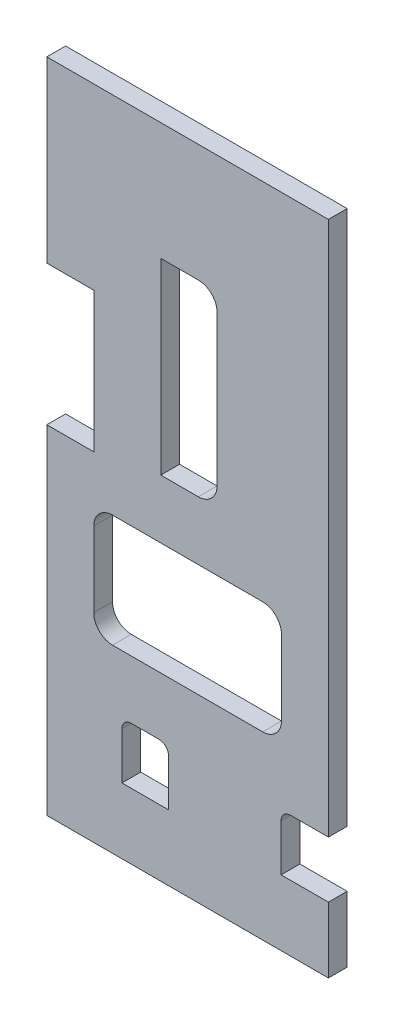
SolidWorks part; units mm, degrees
ref_plane "Front Plane" through (0, 0, 0) normal (0, 0, 1) x (1, 0, 0)
ref_plane "Top Plane" through (0, 0, 0) normal (0, 1, 0) x (1, 0, 0)
ref_plane "Right Plane" through (0, 0, 0) normal (1, 0, 0) x (0, 0, -1)
sketch "Sketch1" plane through (0, 0, 0) normal (0, 0, 1) x (1, 0, 0)
  line L1 (0, 0) -> (95.25, 0)
  line L2 (0, 0) -> (0, 222.25)
  line L3 (0, 222.25) -> (95.25, 222.25)
  line L4 (95.25, 0) -> (95.25, 222.25)
  dimension "D1" = 222.25
  dimension "D2" = 95.25
extrude "Boss-Extrude1" add sketch "Sketch1" along normal blind 6.35
sketch "Sketch2" plane through (0, 0, 0) normal (-1, 0, 0) x (0, 0, 1)
  line L1 (-4.1786, 161.8121) -> (13.515, 161.8121)
  line L2 (-4.1786, 161.8121) -> (-4.1786, 114.4656)
  line L3 (-4.1786, 114.4656) -> (13.515, 114.4656)
  line L4 (13.515, 161.8121) -> (13.515, 114.4656)
extrude "Cut-Extrude1" cut sketch "Sketch2" against normal blind 15.875
sketch "Sketch3" plane through (0, 0, 0) normal (0, 0, -1) x (-1, 0, 0)
  line L0 (-32.2, 118.9831) -> (-38.55, 118.9831) construction
  line L1 (-51.25, 182.4831) -> (-38.55, 182.4831)
  line L2 (-57.6, 176.1331) -> (-57.6, 125.3331)
  line L3 (-51.25, 118.9831) -> (-38.55, 118.9831)
  line L4 (-38.55, 182.4831) -> (-38.55, 118.9831)
  line L5 (-32.2, 118.9831) -> (-32.2, 182.4831) construction
  arc A0 (-57.6, 125.3331) -> (-51.25, 118.9831) centre (-51.25, 125.3331) ccw
  arc A1 (-51.25, 182.4831) -> (-57.6, 176.1331) centre (-51.25, 176.1331) ccw
  point P10 (-57.6, 118.9831)
  point P13 (-57.6, 182.4831)
  dimension "D5" = 6.35
  dimension "D1" = 63.5
  dimension "D2" = 0
  dimension "D3" = 19.05
  dimension "D4" = 6.35
extrude "Cut-Extrude2" cut sketch "Sketch3" against normal blind 6.35
sketch "Sketch4" plane through (0, 0, 0) normal (0, 0, -1) x (-1, 0, 0)
  line L0 (0, 114.4656) -> (0, 0) construction
  line L1 (-73.025, 99.1007) -> (-22.225, 99.1007)
  line L2 (-79.375, 92.7507) -> (-79.375, 67.3507)
  line L3 (-73.025, 61.0007) -> (-22.225, 61.0007)
  line L4 (-15.875, 92.7507) -> (-15.875, 67.3507)
  line L5 (0, 0) -> (-95.25, 0) construction
  arc A0 (-22.225, 61.0007) -> (-15.875, 67.3507) centre (-22.225, 67.3507) ccw
  arc A1 (-79.375, 67.3507) -> (-73.025, 61.0007) centre (-73.025, 67.3507) ccw
  arc A2 (-73.025, 99.1007) -> (-79.375, 92.7507) centre (-73.025, 92.7507) ccw
  arc A3 (-22.225, 99.1007) -> (-15.875, 92.7507) centre (-22.225, 92.7507) cw
  point P10 (-15.875, 61.0007)
  point P13 (-79.375, 61.0007)
  point P18 (-15.875, 99.1007)
  dimension "D5" = 6.35
  dimension "D1" = 63.5
  dimension "D2" = 38.1
  dimension "D3" = 15.875
  dimension "D4" = 61.0007
extrude "Cut-Extrude3" cut sketch "Sketch4" against normal blind 6.35
sketch "Sketch5" plane through (0, 0, 0) normal (0, 0, -1) x (-1, 0, 0)
  line L0 (-95.25, 0) -> (-95.25, 222.25) construction
  line L1 (-95.25, 22.225) -> (-79.248, 22.225)
  line L2 (-95.25, 22.225) -> (-95.25, 41.275)
  line L3 (-95.25, 41.275) -> (-82.423, 41.275)
  line L4 (-25.4, 22.225) -> (-25.4, 38.1)
  line L5 (-95.25, 22.225) -> (0, 22.225) construction
  line L6 (-41.148, 22.225) -> (-25.4, 22.225)
  line L8 (-79.248, 38.1) -> (-79.248, 22.225)
  line L9 (-37.973, 41.275) -> (-28.575, 41.275)
  line L10 (-41.148, 38.1) -> (-41.148, 22.225)
  arc A0 (-28.575, 41.275) -> (-25.4, 38.1) centre (-28.575, 38.1) cw
  arc A1 (-37.973, 41.275) -> (-41.148, 38.1) centre (-37.973, 38.1) ccw
  arc A2 (-82.423, 41.275) -> (-79.248, 38.1) centre (-82.423, 38.1) cw
  point P14 (-25.4, 41.275)
  dimension "D5" = 3.175
  dimension "D1" = 69.85
  dimension "D2" = 19.05
  dimension "D3" = 38.1
  dimension "D4" = 15.748
extrude "Cut-Extrude4" cut sketch "Sketch5" against normal blind 6.35
